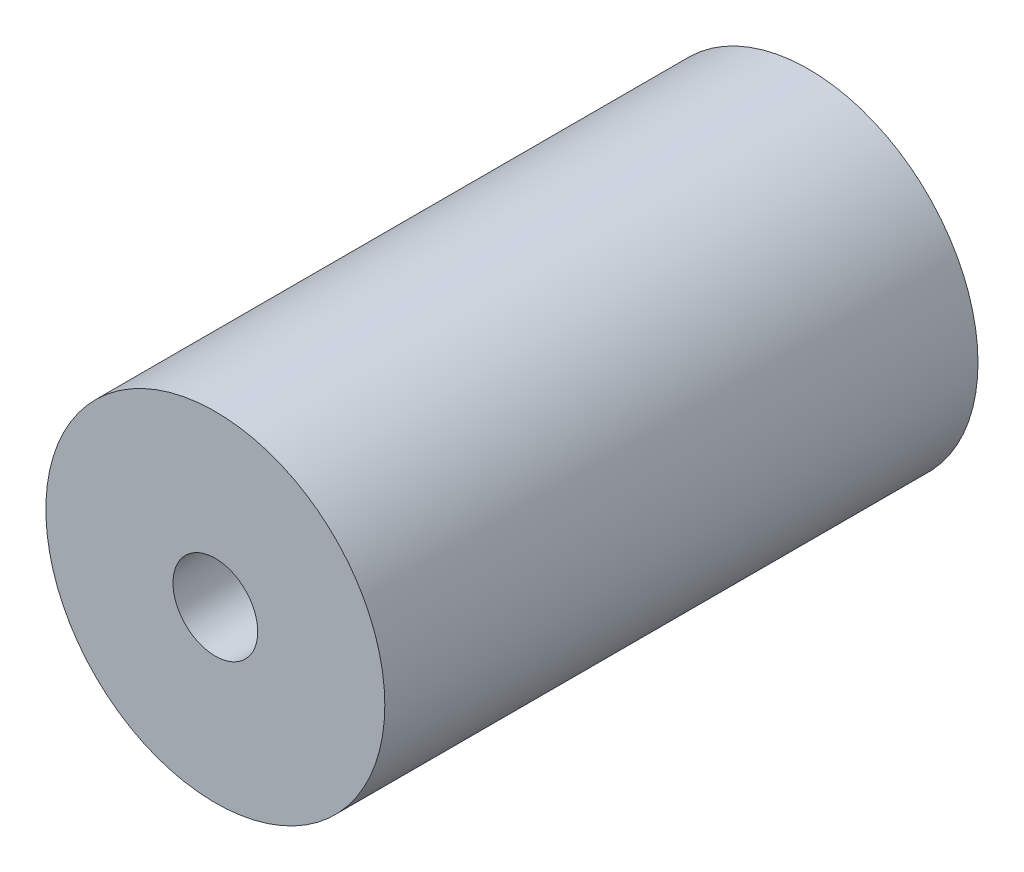
SolidWorks part; units mm, degrees
ref_plane "Alzado" through (0, 0, 0) normal (0, 0, 1) x (1, 0, 0)
ref_plane "Planta" through (0, 0, 0) normal (0, 1, 0) x (1, 0, 0)
ref_plane "Vista lateral" through (0, 0, 0) normal (1, 0, 0) x (0, 0, -1)
sketch "Croquis1" plane through (0, 0, 0) normal (0, 0, 1) x (1, 0, 0)
  circle A0 centre (0, 0) radius 10
  circle A1 centre (0, 0) radius 2.5
  dimension "D1" = 20
  dimension "D2" = 5
extrude "Saliente-Extruir1" add sketch "Croquis1" along normal mid plane 35
